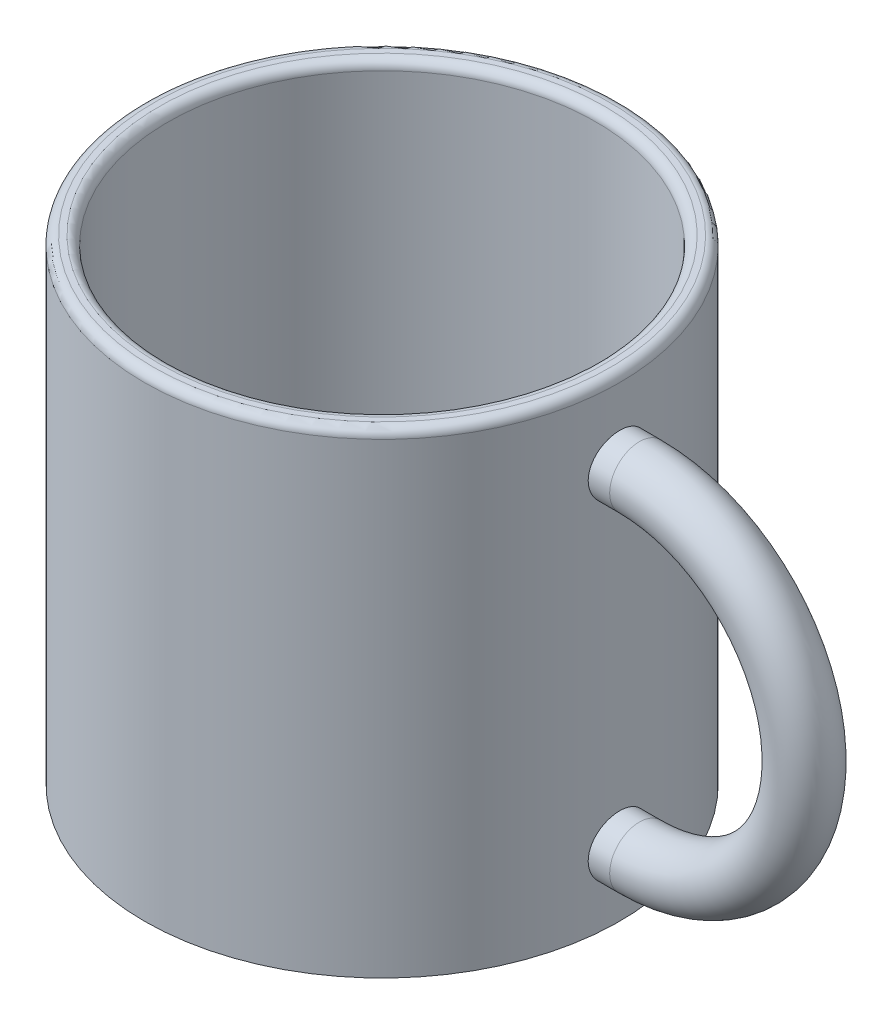
SolidWorks part; units mm, degrees
ref_plane "Front" through (0, 0, 0) normal (0, 0, 1) x (1, 0, 0)
ref_plane "Top" through (0, 0, 0) normal (0, 1, 0) x (1, 0, 0)
ref_plane "Right" through (0, 0, 0) normal (1, 0, 0) x (0, 0, -1)
other "Configuration Table"
sketch "Sketch1" plane through (0, 0, 0) normal (0, 1, 0) x (1, 0, 0)
  circle A0 centre (0, 0) radius 20
  dimension "D1" = 40
extrude "Extrude1" add sketch "Sketch1" along normal blind 40
sketch "Sketch2" plane through (0, 0, 0) normal (1, 0, 0) x (0, 0, -1)
  line L0 (0, 40) -> (0, 0) construction
  circle A0 centre (0, 33.273) radius 2.5
  dimension "D1" = 5
sketch "Sketch3" plane through (0, 0, 0) normal (0, 0, 1) x (1, 0, 0)
  line L0 (0, 30.773) -> (21.65, 30.773)
  line L1 (0, 30.773) -> (0, 35.773) construction
  line L2 (21.65, 8.053) -> (0, 8.053)
  line L3 (0, 40) -> (0, 0) construction
  arc A0 (21.65, 30.773) -> (21.65, 8.053) centre (21.65, 19.413) cw
  dimension "D2" = 11.36
  dimension "D1" = 21.65
sweep "Sweep1" add profiles "Sketch2" path "Sketch3"
sketch "Sketch4" plane through (0, 40, 0) normal (0, 1, 0) x (-1, 0, 0)
  circle A2 centre (0, 0) radius 18
  circle A3 centre (0, 0) radius 18
  dimension "D1" = 2
extrude "Cut-Extrude1" cut sketch "Sketch4" against normal offset from surface (38 mm away) 2 up to face at (0, 0, 20)
fillet "Fillet1" radius 0.75 2 edges at (0, 40, 20) (0, 40, 18)
fillet "Fillet2" radius 0.75 1 edges at (0, 2, 18)
scale "Scale1" scale about centroid uniform scaling yes scale factor 2.5
scale "Scale2" scale about centroid uniform scaling yes scale factor 1.2
